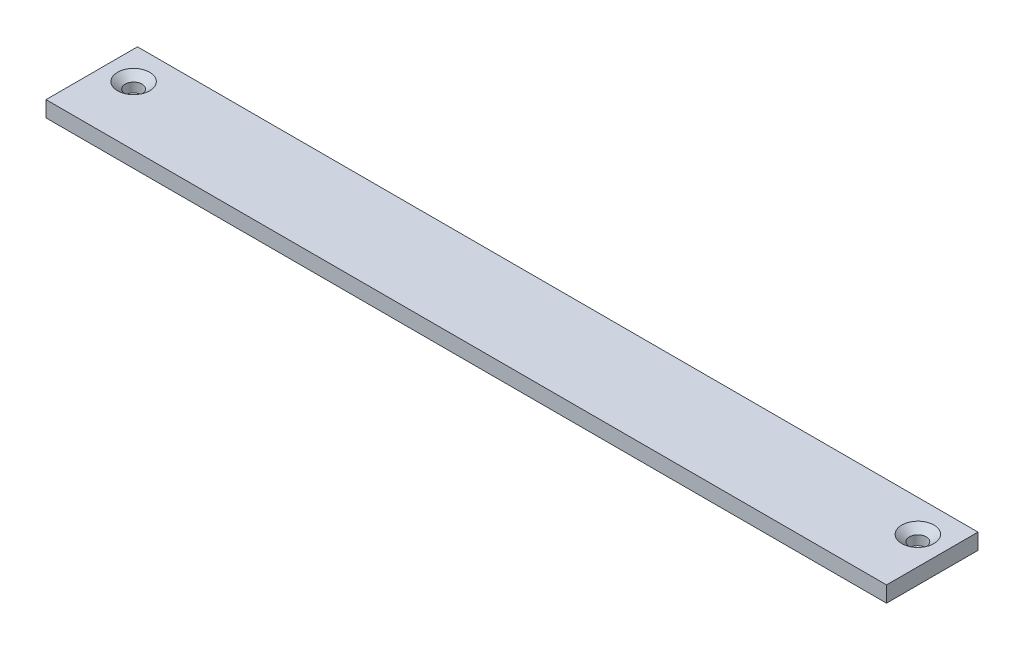
SolidWorks part; units mm, degrees
material "6061-T6 (SS)"
ref_plane "Front Plane" through (0, 0, 0) normal (0, 0, 1) x (1, 0, 0)
ref_plane "Top Plane" through (0, 0, 0) normal (0, 1, 0) x (1, 0, 0)
ref_plane "Right Plane" through (0, 0, 0) normal (1, 0, 0) x (0, 0, -1)
sketch "Sketch1" plane through (0, 0, 0) normal (0, 1, 0) x (1, 0, 0)
  line L1 (-168.275, 23.8125) -> (168.275, 23.8125)
  line L2 (-168.275, 23.8125) -> (-168.275, -23.8125)
  line L3 (-168.275, -23.8125) -> (168.275, -23.8125)
  line L4 (168.275, 23.8125) -> (168.275, -23.8125)
  line L5 (-168.275, 23.8125) -> (168.275, -23.8125) construction
  line L6 (-168.275, -23.8125) -> (168.275, 23.8125) construction
  point P0 (0, 0)
  dimension "D1" = 47.625
  dimension "D2" = 336.55
extrude "Boss-Extrude1" add sketch "Sketch1" along normal mid plane 6.35
hole_wizard "CSK for 1/4 Flat Head Machine Screw (100)1" positions "Sketch2" profile "Sketch3" countersink size "1/4" standard "ANSI Inch" end condition through all
sketch "Sketch2" plane through (0, 3.175, 0) normal (0, 1, 0) x (1, 0, 0)
  line L0 (0, 44.9099) -> (0, -78.0374) construction
  line L2 (-168.275, 23.8125) -> (-168.275, -23.8125) construction
  point P0 (-157.0037, 0)
  point P2 (157.0037, 0)
  dimension "D1" = 11.2712
sketch "Sketch3" plane through (-157.0037, 3.175, 0) normal (1, 0, 0) x (0, 0, 1)
  line L0 (0, 0) -> (0, 6.35)
  line L1 (0, 6.35) -> (3.3782, 6.35)
  line L2 (3.3782, 6.35) -> (3.3782, 2.5682)
  line L3 (3.3782, 2.5682) -> (6.4389, 0)
  line L5 (6.4389, 0) -> (0, 0)
  line L6 (-3.3782, 2.5682) -> (-6.4389, 0) construction
  line L11 (0, -6.35) -> (0, 107.95) construction
  dimension "Thru Hole Dia." = 6.7564
  dimension "Thru Hole Depth" = 6.35
  dimension "Near C'Sink Dia." = 12.8778
  dimension "Near C'Sink Angle" = 100
sketch "Sketch4" plane through (-168.275, 0, 0) normal (-1, 0, 0) x (0, 0, 1)
  line L0 (-23.8125, -3.175) -> (-12.814, 3.175) construction
  line L1 (-23.8125, 3.175) -> (23.8125, 3.175) construction
  line L2 (-12.814, 3.175) -> (-23.8125, 3.175)
  line L3 (-23.8125, 3.175) -> (-23.8125, -3.175)
  line L4 (-12.814, 3.175) -> (-12.814, -3.175)
  line L5 (-23.8125, -3.175) -> (23.8125, -3.175) construction
  line L6 (-12.814, -3.175) -> (-23.8125, -3.175)
  dimension "D1" = 60
extrude "Cut-Extrude1" cut sketch "Sketch4" against normal through all both and the other way through all
sketch "Sketch5" [suppressed] plane through (0, -3.175, 0) normal (0, -1, 0) x (1, 0, 0)
  line L0 (168.275, -23.8125) -> (-168.275, -23.8125) construction
  circle A0 centre (0, -11.1125) radius 3.175
  dimension "D2" = 6.35
  dimension "D1" = 12.7
extrude "Cut-Extrude2" [suppressed] cut sketch "Sketch5" against normal through all both and the other way through all
